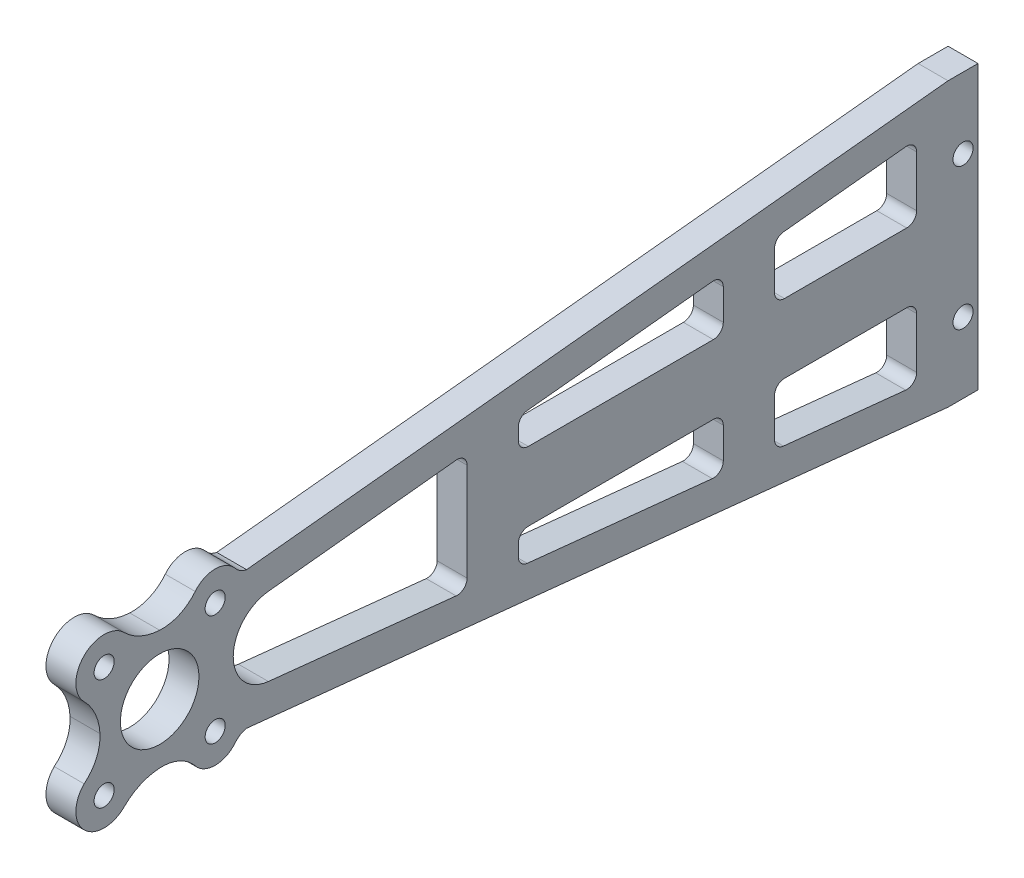
SolidWorks part; units mm, degrees
material "6061-T6 (SS)"
ref_plane "Front Plane" through (0, 0, 0) normal (0, 0, 1) x (1, 0, 0)
ref_plane "Top Plane" through (0, 0, 0) normal (0, 1, 0) x (1, 0, 0)
ref_plane "Right Plane" through (0, 0, 0) normal (1, 0, 0) x (0, 0, -1)
sketch "Sketch1" plane through (0, 0, 0) normal (1, 0, 0) x (0, 0, -1)
  line L0 (0, 0) -> (0, 38.4736) construction
  line L1 (0, 0) -> (-38.4736, 0) construction
  line L2 (0, 0) -> (0, -38.4736) construction
  line L3 (0, 0) -> (130.263, 0) construction
  line L4 (0, 0) -> (27.205, 27.205) construction
  line L5 (0, 0) -> (-27.205, -27.205) construction
  line L6 (0, 0) -> (-27.205, 27.205) construction
  line L7 (0, 0) -> (27.205, -27.205) construction
  line L8 (13.8379, 10.9334) -> (125.5, 22.5)
  line L9 (0, 5.5) -> (143.657, 5.5) construction
  line L10 (13.8423, -10.9339) -> (125.5, -22.5)
  line L11 (125.5, 22.5) -> (130.263, 22.5)
  line L12 (130.263, 22.5) -> (130.263, -22.5)
  line L13 (130.263, -22.5) -> (125.5, -22.5)
  line L14 (0, -5.5) -> (143.657, -5.5) construction
  line L15 (148.4792, 19.8536) -> (9.9118, 5.5) construction
  line L16 (9.9118, -5.5) -> (167.7972, -21.8546) construction
  line L17 (17.302, 6.2153) -> (47.184, 9.3581)
  line L18 (48.9375, 7.7793) -> (48.9375, -7.7793)
  line L19 (47.184, -9.3581) -> (17.302, -6.2154)
  line L25 (57.0937, 8.9558) -> (57.0937, 7.0875)
  line L26 (58.6812, 5.5) -> (88.1312, 5.5)
  line L27 (89.7187, 7.0875) -> (89.7187, 12.0064)
  line L28 (87.9677, 13.5854) -> (58.5177, 10.5349)
  line L29 (58.6812, -5.5) -> (88.1312, -5.5)
  line L30 (89.7187, -7.0875) -> (89.7187, -12.0064)
  line L31 (87.9677, -13.5854) -> (58.5177, -10.5348)
  line L32 (57.0937, -8.9558) -> (57.0937, -7.0875)
  line L33 (99.2989, 14.7592) -> (118.7489, 16.7739)
  line L34 (120.5, 15.1949) -> (120.5, 7.0875)
  line L35 (118.9125, 5.5) -> (99.4625, 5.5)
  line L36 (97.875, 7.0875) -> (97.875, 13.1801)
  line L37 (118.9125, -5.5) -> (99.4625, -5.5)
  line L38 (97.875, -7.0875) -> (97.875, -13.1801)
  line L39 (99.2989, -14.7592) -> (118.7489, -16.7739)
  line L40 (120.5, -15.1949) -> (120.5, -7.0875)
  arc A0 (118.9125, 5.5) -> (120.5, 7.0875) centre (118.9125, 7.0875) ccw
  arc A1 (120.5, 15.1949) -> (118.7489, 16.7739) centre (118.9125, 15.1949) ccw
  arc A2 (99.4625, 5.5) -> (97.875, 7.0875) centre (99.4625, 7.0875) cw
  arc A3 (97.875, 13.1801) -> (99.2989, 14.7592) centre (99.4625, 13.1801) cw
  arc A4 (89.7187, 12.0064) -> (87.9677, 13.5854) centre (88.1312, 12.0064) ccw
  arc A5 (-12.0208, 5.6568) -> (-5.6565, 12.0205) centre (-8.8386, 8.8386) cw
  arc A6 (-5.6569, -12.0209) -> (-12.0209, -5.6569) centre (-8.8389, -8.8389) cw
  arc A7 (-5.6565, 12.0205) -> (0, 9.5) centre (0.4572, 18.1336) ccw
  arc A8 (0, 9.5) -> (5.6556, 12.0196) centre (0.3601, 16.2991) ccw
  arc A9 (5.6556, 12.0196) -> (12.0208, 12.0208) centre (8.8387, 9.4473) cw
  arc A10 (12.0208, 12.0208) -> (13.8379, 10.9334) centre (14.412, 13.9547) ccw
  arc A11 (-12.0208, 5.6568) -> (-9.5, 0) centre (-18.1368, -0.4586) cw
  arc A12 (-9.5, 0) -> (-12.0209, -5.6569) centre (-16.2975, -0.361) cw
  arc A13 (-5.6569, -12.0209) -> (0, -9.5) centre (0.4584, -18.1361) cw
  arc A14 (0, -9.5) -> (5.6592, -12.0232) centre (0.3608, -16.2988) cw
  arc A15 (5.6592, -12.0232) -> (12.0208, -12.0208) centre (8.8391, -9.4572) ccw
  arc A16 (12.0208, -12.0208) -> (13.8423, -10.9339) centre (14.3996, -13.9375) cw
  arc A17 (89.7187, 7.0875) -> (88.1312, 5.5) centre (88.1312, 7.0875) cw
  arc A18 (58.6812, 5.5) -> (57.0937, 7.0875) centre (58.6812, 7.0875) cw
  arc A19 (57.0937, 8.9558) -> (58.5177, 10.5349) centre (58.6812, 8.9558) cw
  arc A20 (47.184, -9.3581) -> (48.9375, -7.7793) centre (47.35, -7.7793) ccw
  arc A21 (48.9375, 7.7793) -> (47.184, 9.3581) centre (47.35, 7.7793) ccw
  arc A23 (120.5, -7.0875) -> (118.9125, -5.5) centre (118.9125, -7.0875) ccw
  arc A24 (120.5, -15.1949) -> (118.7489, -16.7739) centre (118.9125, -15.1949) cw
  arc A25 (99.2989, -14.7592) -> (97.875, -13.1801) centre (99.4625, -13.1801) cw
  arc A26 (97.875, -7.0875) -> (99.4625, -5.5) centre (99.4625, -7.0875) cw
  arc A27 (88.1312, -5.5) -> (89.7187, -7.0875) centre (88.1312, -7.0875) cw
  arc A28 (89.7187, -12.0064) -> (87.9677, -13.5854) centre (88.1312, -12.0064) cw
  arc A29 (58.5177, -10.5348) -> (57.0937, -8.9558) centre (58.6812, -8.9558) cw
  arc A30 (57.0937, -7.0875) -> (58.6812, -5.5) centre (58.6812, -7.0875) cw
  arc A31 (17.302, -6.2154) -> (17.302, 6.2153) centre (17.9593, 0) cw
  circle A34 centre (0, 0) radius 6.25
  point P12 (120.5, 5.5)
  point P16 (120.5, 16.9553)
  point P19 (-5.6565, 12.0205)
  point P20 (5.6556, 12.0196)
  point P23 (5.6592, -12.0232)
  point P24 (-5.6569, -12.0209)
  point P25 (-12.0209, -5.6569)
  point P26 (-12.0208, 5.6568)
  point P27 (-12.0208, 12.0208)
  point P28 (12.0208, 12.0208)
  point P29 (12.0208, -12.0208)
  point P30 (-12.0208, -12.0208)
  point P38 (13.8423, -10.9339)
  point P39 (13.8379, 10.9334)
  point P43 (0, 9.5)
  point P44 (-9.5, 0)
  point P45 (0, -9.5)
  point P63 (127.8815, 22.5)
  point P64 (127.8815, -22.5)
  point P66 (97.875, 5.5)
  point P69 (0, 5.5)
  point P70 (-13.3386, 8.8386)
  point P71 (-13.3389, -8.8389)
  point P76 (97.875, 0)
  point P77 (32.625, 0)
  point P80 (9.9118, -5.5)
  point P81 (-13.3389, 0)
  point P84 (120.5, 16.9553)
  point P85 (48.9375, 0)
  point P86 (120.5, -16.9553)
  point P87 (81.5625, 0)
  point P88 (114.1875, 0)
  point P89 (16.3125, 0)
  point P90 (73.4062, 0)
  point P91 (89.7187, 0)
  point P92 (57.0937, 0)
  point P93 (40.7812, 0)
  point P94 (24.4687, 0)
  point P95 (106.0312, 0)
  point P96 (48.9375, 9.5425)
  point P102 (48.9375, -9.5425)
  point P103 (48.9375, -9.5425)
  point P104 (48.9375, -5.5)
  point P107 (57.0937, 5.5)
  point P108 (48.9375, 9.5425)
  point P110 (57.0937, 10.3874)
  point P111 (89.7187, 5.5)
  point P112 (89.7187, 13.7668)
  point P115 (57.0937, -5.5)
  point P118 (57.0937, -10.3873)
  point P119 (89.7187, -13.7668)
  point P120 (89.7187, -5.5)
  point P123 (120.5, 5.5)
  point P126 (120.5, -5.5)
  point P127 (97.875, 14.6117)
  point P128 (97.875, 5.5)
  point P131 (97.875, -5.5)
  point P132 (97.875, 14.6117)
  point P134 (97.875, -14.6117)
  point P140 (89.7187, 13.7668)
  point P143 (89.7187, 5.5)
  point P146 (57.0937, 5.5)
  point P149 (57.0937, 10.3874)
  point P150 (12.0209, -5.6569)
  point P152 (48.9375, 5.5)
  point P155 (48.9375, 9.5425)
  point P161 (120.5, -5.5)
  point P164 (120.5, -16.9553)
  point P167 (97.875, -14.6117)
  point P170 (97.875, -5.5)
  point P173 (89.7187, -5.5)
  point P176 (89.7187, -13.7668)
  point P179 (57.0937, -10.3873)
  point P182 (57.0937, -5.5)
  point P184 (12.0208, 5.6568)
  point P188 (48.9375, -9.5425)
  point P191 (48.9375, -5.5)
  dimension "D1" = 1.5875
  dimension "D3" = 4.763
  dimension "D2" = 1.5875
  dimension "D7" = 1.5875
  dimension "D8" = 6.25
  dimension "D4" = 130.263
  dimension "D5" = 45
  dimension "D6" = 143.6019
extrude "Boss-Extrude1" add sketch "Sketch1" along normal mid plane 4.763
hole_wizard "M3 Clearance Hole1" positions "Sketch3" profile "Sketch2" hole size "M3" standard "ANSI Metric" end condition through all
sketch "Sketch3" plane through (2.3815, 0, 0) normal (1, 0, 0) x (0, 0, -1)
  line L3 (127.8815, 22.5) -> (127.8815, -22.5) construction
  line L4 (130.263, 22.5) -> (125.5, 22.5) construction
  line L5 (125.5, -22.5) -> (130.263, -22.5) construction
  point P0 (127.8815, 11.25)
  point P2 (127.8815, -11.25)
  dimension "D1" = 11.25
  dimension "D2" = 11.25
sketch "Sketch2" plane through (2.3815, 11.25, -127.8815) normal (0, 1, 0) x (0, 0, -1)
  line L0 (0, 0) -> (0, 4.763)
  line L1 (0, 4.763) -> (1.6, 4.763)
  line L2 (1.6, 4.763) -> (1.6, 0)
  line L5 (1.6, 0) -> (0, 0)
  line L11 (0, -6.35) -> (0, 107.95) construction
  dimension "Thru Hole Dia." = 3.2
  dimension "Thru Hole Depth" = 4.763
hole_wizard "M3 Clearance Hole2" positions "Sketch5" profile "Sketch4" hole size "M3" standard "ANSI Metric" end condition through all
sketch "Sketch5" plane through (2.3815, 0, 0) normal (1, 0, 0) x (0, 0, -1)
  point P0 (-8.8388, 8.8388)
  point P2 (8.8388, 8.8388)
  point P4 (8.8388, -8.8388)
  point P6 (-8.8388, -8.8388)
  dimension "D2" = 17.6777
  dimension "D3" = 25
sketch "Sketch4" plane through (2.3815, 8.8388, 8.8388) normal (0, 1, 0) x (0, 0, -1)
  line L0 (0, 0) -> (0, 4.763)
  line L1 (0, 4.763) -> (1.6, 4.763)
  line L2 (1.6, 4.763) -> (1.6, 0)
  line L5 (1.6, 0) -> (0, 0)
  line L11 (0, -6.35) -> (0, 107.95) construction
  dimension "Thru Hole Dia." = 3.2
  dimension "Thru Hole Depth" = 4.763
